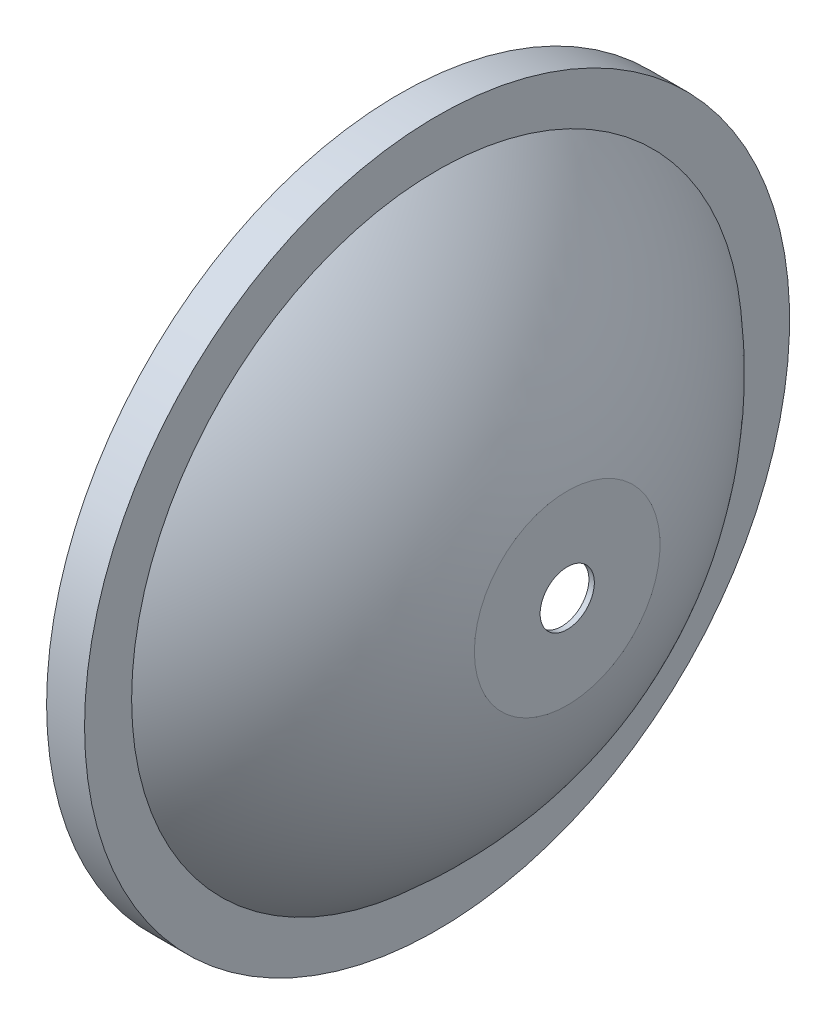
SolidWorks part; units mm, degrees
ref_plane "Front Plane" through (0, 0, 0) normal (0, 0, 1) x (1, 0, 0)
ref_plane "Top Plane" through (0, 0, 0) normal (0, 1, 0) x (1, 0, 0)
ref_plane "Right Plane" through (0, 0, 0) normal (1, 0, 0) x (0, 0, -1)
sketch "Sketch1" plane through (0, 0, 0) normal (0, 0, 1) x (1, 0, 0)
  line L0 (-110.4164, 0) -> (56.8462, 0) construction
  line L1 (-29.993, 64) -> (-23.993, 64)
  line L2 (-23.993, 64) -> (-23.993, 55.857)
  line L3 (0, 5) -> (0, 17)
  line L4 (-29.993, 65) -> (-22.993, 65)
  line L5 (-22.993, 65) -> (-22.993, 56.3205)
  line L6 (1, 5) -> (1, 17.1177)
  line L7 (-29.993, 65) -> (-29.993, 64)
  line L8 (0, 5) -> (1, 5)
  arc A0 (-23.993, 55.857) -> (0, 17) centre (-70.993, 0) cw
  arc A1 (-22.993, 56.3205) -> (1, 17.1177) centre (-70.993, 0) cw
  dimension "D6" = 73
  dimension "D1" = 6
  dimension "D2" = 64
  dimension "D3" = 12
  dimension "D4" = 5
  dimension "D5" = 41
  dimension "D7" = 1
revolve "Revolve1" add sketch "Sketch1" angle 360 about L0
